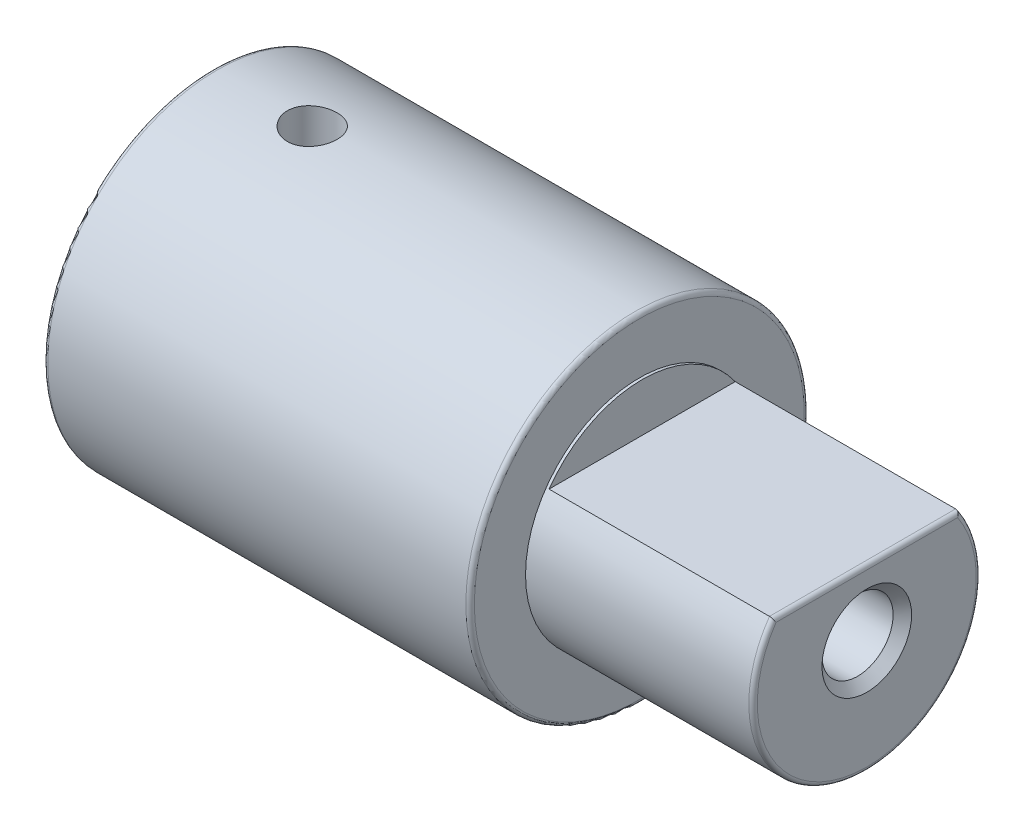
SolidWorks part; units mm, degrees
ref_plane "Front Plane" through (0, 0, 0) normal (0, 0, 1) x (1, 0, 0)
ref_plane "Top Plane" through (0, 0, 0) normal (0, 1, 0) x (1, 0, 0)
ref_plane "Right Plane" through (0, 0, 0) normal (1, 0, 0) x (0, 0, -1)
sketch "Sketch2" plane through (0, 0, 0) normal (0, 1, 0) x (1, 0, 0)
  line L0 (0, 0) -> (23, 0) construction
  line L1 (0, 2.5) -> (13.1, 2.5)
  line L2 (13.1, 2.5) -> (13.1, 0)
  line L3 (13.1, 0) -> (23, 0)
  line L4 (23, 0) -> (23, 4)
  line L5 (23, 4) -> (15, 4)
  line L6 (15, 4) -> (15, 5.95)
  line L7 (15, 5.95) -> (0, 5.95)
  line L8 (0, 5.95) -> (0, 2.5)
  point P10 (23, -4)
  point P11 (0, -5.95)
  point P12 (0, -2.5)
  dimension "D1" = 11.9
  dimension "D2" = 5
  dimension "D3" = 13.1
  dimension "D4" = 15
  dimension "D5" = 8
  dimension "D6" = 8
revolve "Revolve1" add sketch "Sketch2" angle 360 about L0
sketch "Sketch3" plane through (23, 0, 0) normal (1, 0, 0) x (0, 0, -1)
  line L0 (-3.2726, 2.3) -> (3.2726, 2.3)
  circle A0 centre (0, 0) radius 4 construction
  arc A1 (-3.2726, 2.3) -> (3.2726, 2.3) centre (0, 0) cw
  circle A2 centre (0, 0) radius 4 construction
  point P5 (0, -4)
  dimension "D1" = 6.3
extrude "Cut-Extrude1" cut sketch "Sketch3" against normal blind 7.9
sketch "Sketch4" plane through (23, 0, 0) normal (1, 0, 0) x (0, 0, -1)
  point P0 (0, 0)
hole_wizard "M3 Tapped Hole1" positions "3DSketch1" profile "Sketch5" tap size "M3" standard "ISO" end condition through all
sketch3d "3DSketch1"
  point P0 (23, 0, 0)
cosmetic thread "Hole Thread1" parameters "D2"=3
sketch "Sketch5" plane through (23, 0, 0) normal (0, 1, 0) x (0, 0, -1)
  line L0 (0, 0) -> (0, 23)
  line L1 (0, 23) -> (1.25, 23)
  line L2 (1.25, 23) -> (1.25, 0.325)
  line L3 (1.25, 0.325) -> (1.575, 0)
  line L5 (1.575, 0) -> (0, 0)
  line L6 (-1.25, 0.325) -> (-1.575, 0) construction
  line L11 (0, -6.35) -> (0, 107.95) construction
  dimension "Thru Tap Drill Dia." = 2.5
  dimension "Thru Tap Drill Depth" = 23
  dimension "Near C'Sink Dia." = 3.15
  dimension "Near C'Sink Angle" = 90
fillet "Fillet1" radius 0.15 5 edges at (15, 0, 5.95) (23, 2.3, 0) (23, -4, 0) (0, 0, 5.95) (0, 0, 2.5)
ref_plane "Plane1" through (0, 5.95, 0) normal (0, 1, 0) x (1, 0, 0)
sketch "Sketch6" plane through (0, 5.95, 0) normal (0, 1, 0) x (1, 0, 0)
  line L0 (3.5, 0) -> (0, 0) construction
  circle A0 centre (3.5, 0) radius 0.875
  dimension "D2" = 1.75
  dimension "D1" = 3.5
extrude "Cut-Extrude2" cut sketch "Sketch6" against normal blind 6
